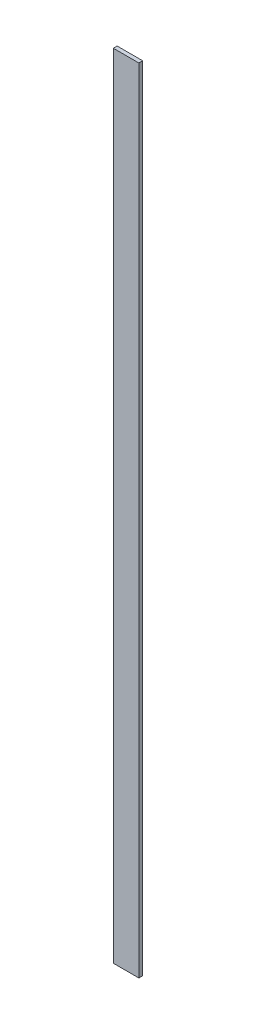
SolidWorks part; units mm, degrees
ref_plane "Front Plane" through (0, 0, 0) normal (0, 0, 1) x (1, 0, 0)
ref_plane "Top Plane" through (0, 0, 0) normal (0, 1, 0) x (1, 0, 0)
ref_plane "Right Plane" through (0, 0, 0) normal (1, 0, 0) x (0, 0, -1)
sketch "Sketch1" plane through (0, 0, -52.8112) normal (0, 0, 1) x (1, 0, 0)
  line L1 (-294.2931, 720) -> (-314.2931, 720)
  line L2 (-294.2931, 720) -> (-294.2931, 100)
  line L3 (-294.2931, 100) -> (-314.2931, 100)
  line L4 (-314.2931, 720) -> (-314.2931, 100)
  line L6 (-314.2931, 0) -> (-314.2931, 1225) construction
  dimension "D1" = 620
  dimension "D2" = 20
extrude "Boss-Extrude1" add sketch "Sketch1" along normal blind 3
